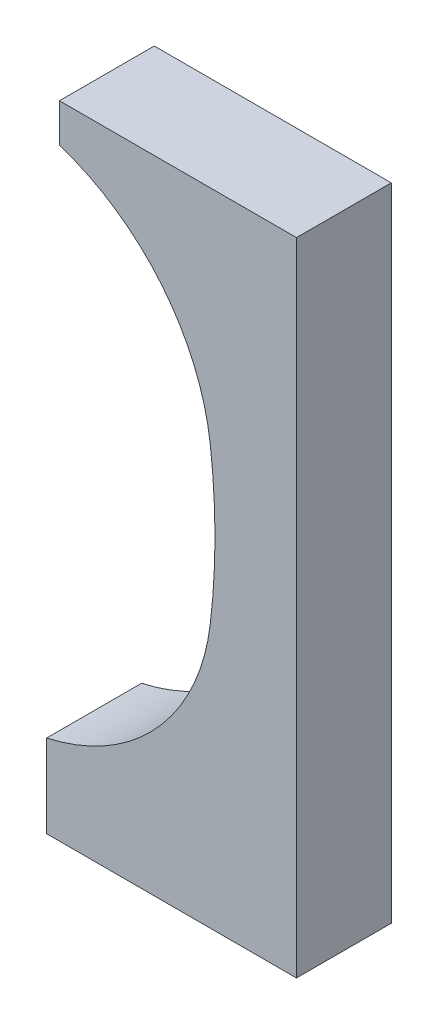
SolidWorks part; units mm, degrees
ref_plane "Спереди" through (0, 0, 0) normal (0, 0, 1) x (1, 0, 0)
ref_plane "Сверху" through (0, 0, 0) normal (0, 1, 0) x (1, 0, 0)
ref_plane "Справа" through (0, 0, 0) normal (1, 0, 0) x (0, 0, -1)
other "Configuration Table"
sketch "Эскиз1" plane through (0, 0, 0) normal (0, 0, 1) x (1, 0, 0)
  line L1 (4.2996, 175.4028) -> (4.2996, 188.4028)
  line L4 (84.2996, 0) -> (84.2996, 175.4028)
  line L6 (84.2996, 175.4028) -> (84.2996, 188.4028)
  line L7 (84.2996, 188.4028) -> (4.2996, 188.4028)
  line L11 (0, 0) -> (0, -28)
  line L12 (84.2996, 0) -> (84.2996, -28)
  line L13 (84.2996, -28) -> (0, -28)
  arc A0 (0, 0) -> (55.1731, 60.6624) centre (-15.2954, 69.3329) ccw
  arc A1 (55.1731, 113.6624) -> (4.2996, 175.4028) centre (-18.7693, 104.5645) ccw
  arc A2 (55.1731, 60.6624) -> (55.1731, 113.6624) centre (-160.2027, 87.1624) ccw
  dimension "D1" = 142
  dimension "D3" = 149
  dimension "D5" = 53
  dimension "D6" = 217
  dimension "D2" = 82
  dimension "D4" = 80
  dimension "D7" = 125.5129
  dimension "D8" = 126.3456
  dimension "D9" = 15.2954
  dimension "D10" = 69.3329
  dimension "D11" = 160.2027
  dimension "D12" = 87.1624
  dimension "D13" = 104.5645
  dimension "D14" = 18.7693
  dimension "D15" = 4.2996
  dimension "D16" = 175.4028
  dimension "D17" = 80
  dimension "D18" = 175.4028
  dimension "D19" = 13
  dimension "D20" = 28
  dimension "D21" = 84.2996
  dimension "D22" = 28
  dimension "D23" = 216.4028
extrude "Бобышка-Вытянуть4" add sketch "Эскиз1" along normal blind 32
